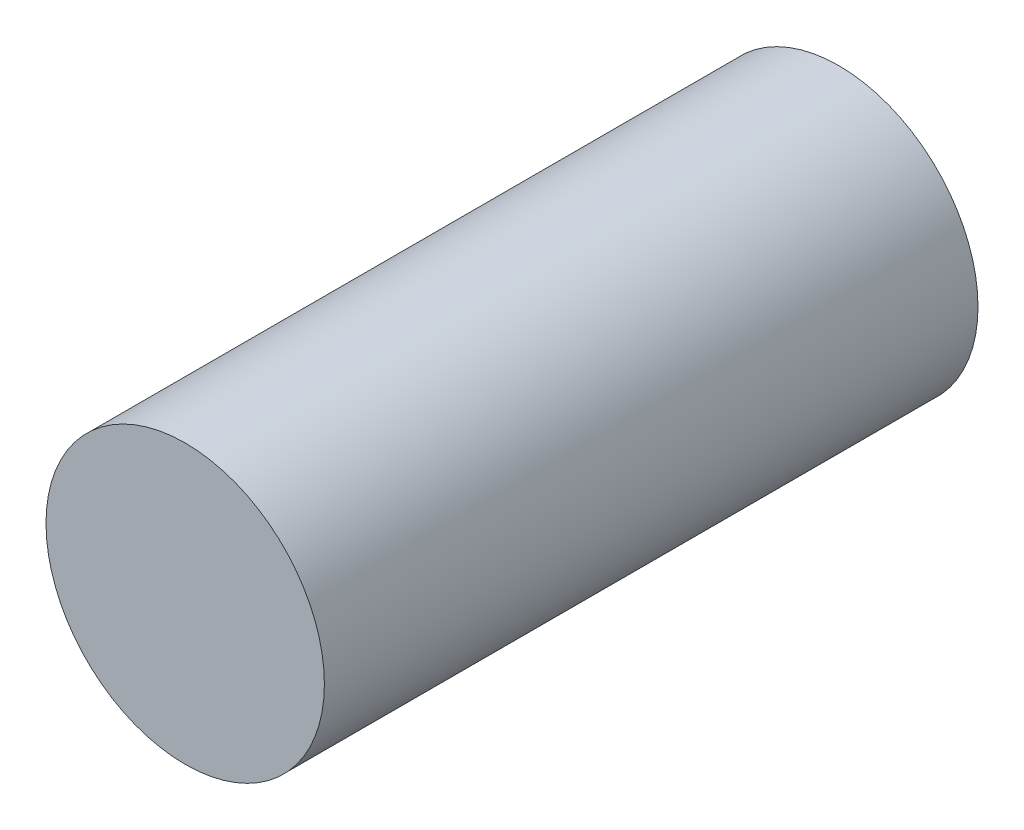
SolidWorks part; units mm, degrees
material "Mousse de polyuréthane flexible"
ref_plane "Face" through (0, 0, 0) normal (0, 0, 1) x (1, 0, 0)
ref_plane "Dessus" through (0, 0, 0) normal (0, 1, 0) x (1, 0, 0)
ref_plane "Droite" through (0, 0, 0) normal (1, 0, 0) x (0, 0, -1)
sketch "Esquisse1" plane through (0, 0, 0) normal (0, 0, 1) x (1, 0, 0)
  circle A0 centre (0, 0) radius 5.75
  dimension "D1" = 11.5
extrude "Boss.-Extru.1" add sketch "Esquisse1" along normal mid plane 27
